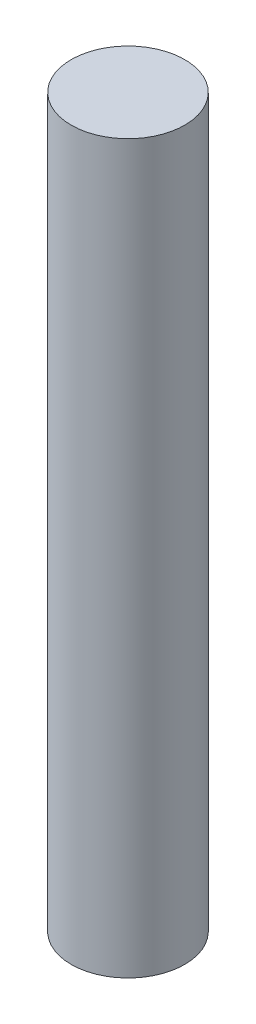
SolidWorks part; units mm, degrees
ref_plane "Front Plane" through (0, 0, 0) normal (0, 0, 1) x (1, 0, 0)
ref_plane "Top Plane" through (0, 0, 0) normal (0, 1, 0) x (1, 0, 0)
ref_plane "Right Plane" through (0, 0, 0) normal (1, 0, 0) x (0, 0, -1)
sketch "Sketch1" plane through (0, 0, 0) normal (0, 1, 0) x (1, 0, 0)
  circle A0 centre (0, 0) radius 3.9688
  dimension "D1" = 7.9375
extrude "Boss-Extrude1" add sketch "Sketch1" along normal blind 50.8
